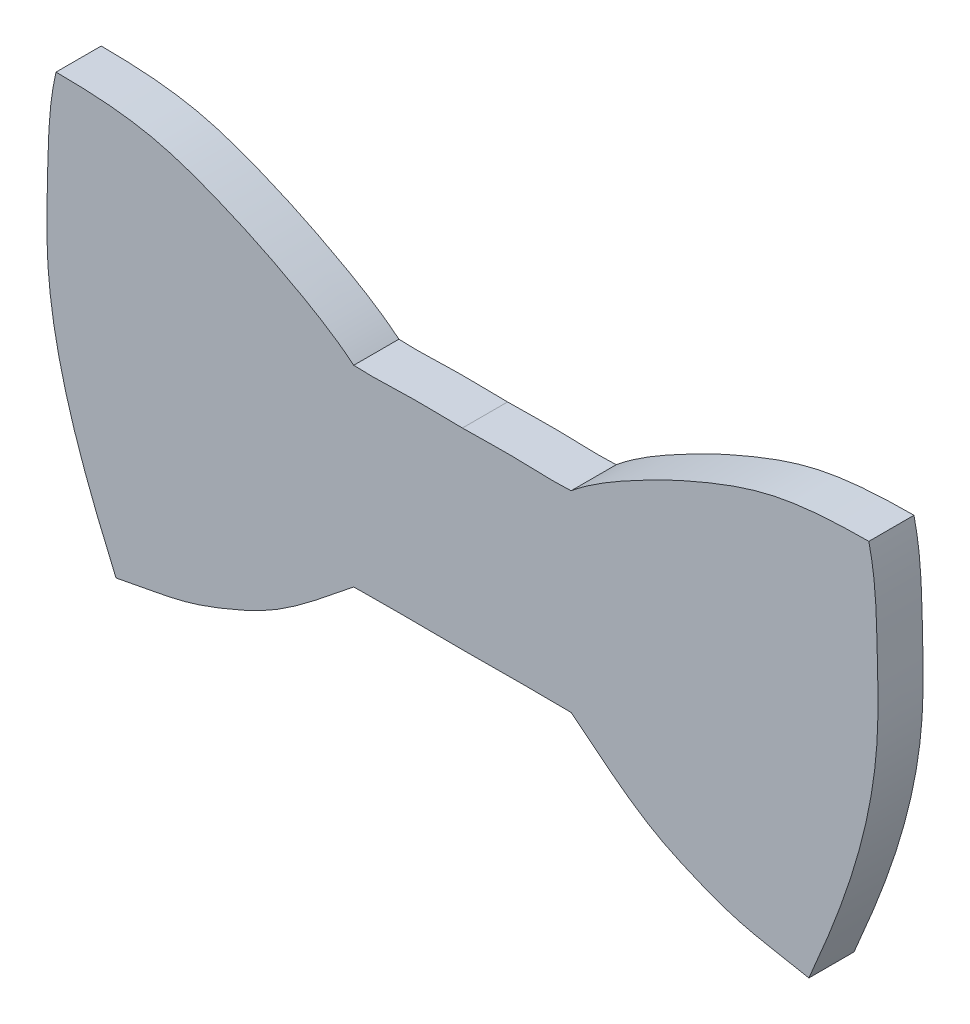
SolidWorks part; units mm, degrees
ref_plane "Front Plane" through (0, 0, 0) normal (0, 0, 1) x (1, 0, 0)
ref_plane "Top Plane" through (0, 0, 0) normal (0, 1, 0) x (1, 0, 0)
ref_plane "Right Plane" through (0, 0, 0) normal (1, 0, 0) x (0, 0, -1)
sketch "Sketch1" plane through (0, 0, 0) normal (0, 0, 1) x (1, 0, 0)
  line L0 (-28.575, 0) -> (28.575, 0) construction
  line L1 (0, 0) -> (0, 8.971) construction
  line L2 (0, 6.2395) -> (0, -7.2607)
  spline S0 degree 3 poles (28.575, 13.6267) (26.1998, 13.6206) (22.1867, 13.4209) (17.8321, 11.8042) (14.6462, 10.4307) (11.4567, 8.8014) (8.9373, 7.3113) (7.6417, 6.2395) knots 0 0 0 0 0.316578 0.524803 0.612692 0.777336 1 1 1 1
  spline S1 degree 3 poles (28.575, 13.6267) (29.1022, 11.3974) (29.134, 7.6205) (29.2916, 2.6455) (28.813, -1.9754) (27.8199, -6.0302) (26.2471, -10.627) (25.1117, -13.3275) (24.3606, -15.0706) knots 0 0 0 0 0.230911 0.383733 0.505873 0.702268 0.806837 1 1 1 1
  spline S2 degree 3 poles (24.3606, -15.0706) (22.6951, -14.7128) (19.9128, -14.3623) (16.3732, -13.0132) (12.2247, -11.1264) (9.5799, -8.7862) (7.6417, -7.2607) knots 0 0 0 0 0.273274 0.444401 0.604132 1 1 1 1
  spline S3 degree 3 poles (7.6417, 6.2395) (6.1725, 6.1513) (3.6263, 6.358) (1.0788, 6.2235) (0, 6.2395) knots 0 0 0 0 0.576548 1 1 1 1
  spline S4 degree 3 poles (7.6417, -7.2607) (6.1732, -7.2443) (3.6258, -7.2267) (1.0787, -7.2655) (0, -7.2607) knots 0 0 0 0 0.576526 1 1 1 1
  dimension "D1" = 57.15
extrude "Boss-Extrude1" add sketch "Sketch1" along normal blind 3.175
mirror "Mirror1" about plane through (0, 0, 0) normal (1, 0, 0) of "Boss-Extrude1"
